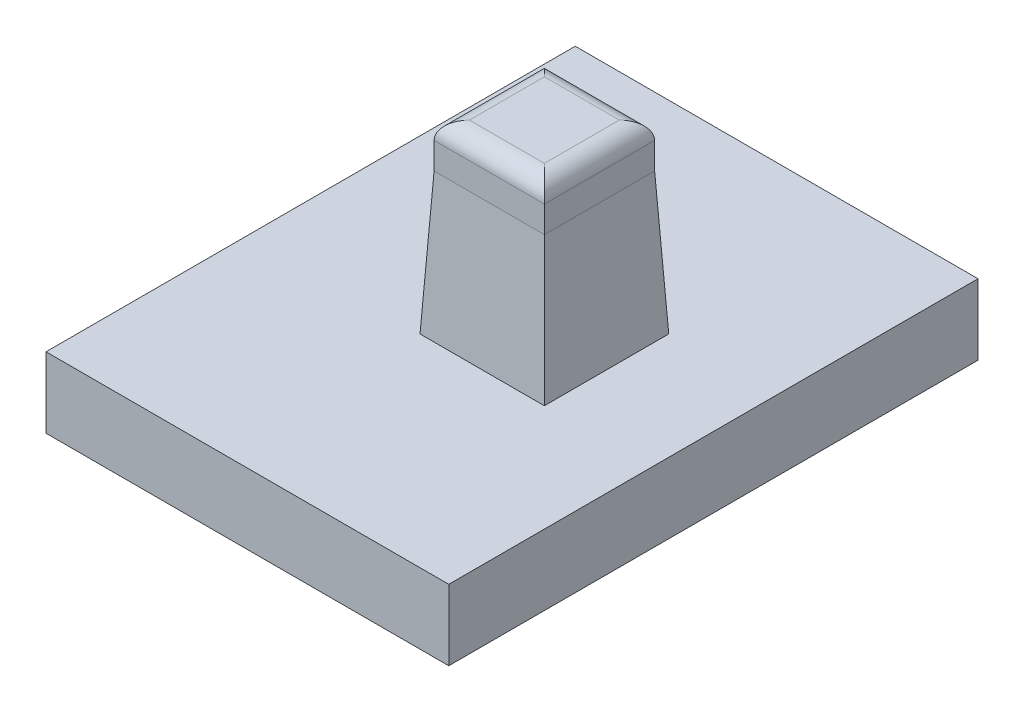
SolidWorks part; units mm, degrees
ref_plane "Front Plane" through (0, 0, 0) normal (0, 0, 1) x (1, 0, 0)
ref_plane "Top Plane" through (0, 0, 0) normal (0, 1, 0) x (1, 0, 0)
ref_plane "Right Plane" through (0, 0, 0) normal (1, 0, 0) x (0, 0, -1)
sketch "Sketch1" plane through (0, 0, 0) normal (0, 1, 0) x (1, 0, 0)
  line L0 (0, 15) -> (13.25, 15) construction
  line L1 (0, 0) -> (240, 0)
  line L2 (0, 0) -> (0, 30)
  line L3 (0, 30) -> (240, 30)
  line L4 (240, 0) -> (240, 30)
  line L5 (0, 0) -> (240, 30) construction
  line L6 (0, 30) -> (240, 0) construction
  line L7 (13.25, 15) -> (43.75, 15) construction
  line L8 (43.75, 15) -> (74.25, 15) construction
  line L9 (74.25, 15) -> (104.75, 15) construction
  line L10 (104.75, 15) -> (135.25, 15) construction
  line L11 (135.25, 15) -> (165.75, 15) construction
  line L12 (165.75, 15) -> (196.25, 15) construction
  line L14 (10.125, 18.125) -> (16.375, 18.125)
  line L15 (10.125, 18.125) -> (10.125, 11.875)
  line L16 (10.125, 11.875) -> (16.375, 11.875)
  line L17 (16.375, 18.125) -> (16.375, 11.875)
  line L18 (10.125, 18.125) -> (16.375, 11.875) construction
  line L19 (10.125, 11.875) -> (16.375, 18.125) construction
  line L23 (196.25, 15) -> (226.75, 15) construction
  line L24 (40.625, 18.125) -> (46.875, 18.125)
  line L25 (40.625, 18.125) -> (40.625, 11.875)
  line L26 (40.625, 11.875) -> (46.875, 11.875)
  line L27 (46.875, 18.125) -> (46.875, 11.875)
  line L28 (40.625, 18.125) -> (46.875, 11.875) construction
  line L29 (40.625, 11.875) -> (46.875, 18.125) construction
  line L30 (71.125, 18.125) -> (77.375, 18.125)
  line L31 (71.125, 18.125) -> (71.125, 11.875)
  line L32 (71.125, 11.875) -> (77.375, 11.875)
  line L33 (77.375, 18.125) -> (77.375, 11.875)
  line L34 (71.125, 18.125) -> (77.375, 11.875) construction
  line L35 (71.125, 11.875) -> (77.375, 18.125) construction
  line L36 (101.625, 18.125) -> (107.875, 18.125)
  line L37 (101.625, 18.125) -> (101.625, 11.875)
  line L38 (101.625, 11.875) -> (107.875, 11.875)
  line L39 (107.875, 18.125) -> (107.875, 11.875)
  line L40 (101.625, 18.125) -> (107.875, 11.875) construction
  line L41 (101.625, 11.875) -> (107.875, 18.125) construction
  line L42 (132.125, 18.125) -> (138.375, 18.125)
  line L43 (132.125, 18.125) -> (132.125, 11.875)
  line L44 (132.125, 11.875) -> (138.375, 11.875)
  line L45 (138.375, 18.125) -> (138.375, 11.875)
  line L46 (132.125, 18.125) -> (138.375, 11.875) construction
  line L47 (132.125, 11.875) -> (138.375, 18.125) construction
  line L48 (162.625, 18.125) -> (168.875, 18.125)
  line L49 (162.625, 18.125) -> (162.625, 11.875)
  line L50 (162.625, 11.875) -> (168.875, 11.875)
  line L51 (168.875, 18.125) -> (168.875, 11.875)
  line L52 (162.625, 18.125) -> (168.875, 11.875) construction
  line L53 (162.625, 11.875) -> (168.875, 18.125) construction
  line L54 (226.75, 15) -> (240, 15) construction
  line L56 (193.125, 18.125) -> (199.375, 18.125)
  line L57 (193.125, 18.125) -> (193.125, 11.875)
  line L58 (193.125, 11.875) -> (199.375, 11.875)
  line L59 (199.375, 18.125) -> (199.375, 11.875)
  line L60 (193.125, 18.125) -> (199.375, 11.875) construction
  line L61 (193.125, 11.875) -> (199.375, 18.125) construction
  line L62 (223.625, 18.125) -> (229.875, 18.125)
  line L63 (223.625, 18.125) -> (223.625, 11.875)
  line L64 (223.625, 11.875) -> (229.875, 11.875)
  line L65 (229.875, 18.125) -> (229.875, 11.875)
  line L66 (223.625, 18.125) -> (229.875, 11.875) construction
  line L67 (223.625, 11.875) -> (229.875, 18.125) construction
  point P4 (120, 15)
  point P14 (0, 15)
  point P18 (13.25, 15)
  point P24 (43.75, 15)
  point P28 (74.25, 15)
  point P33 (104.75, 15)
  point P38 (135.25, 15)
  point P43 (165.75, 15)
  point P55 (196.25, 15)
  point P56 (226.75, 15)
  dimension "D1" = 6.25
  dimension "D2" = 30.5
  dimension "D3" = 240
  dimension "D4" = 30
extrude "Boss-Extrude1" add sketch "Sketch1" along normal blind 4
sketch "Sketch2" plane through (0, 4, 0) normal (0, 1, 0) x (1, 0, 0)
  line L0 (193.125, 11.875) -> (199.375, 11.875) construction
  line L1 (10.125, 18.125) -> (16.375, 18.125)
  line L2 (10.125, 18.125) -> (10.125, 11.875)
  line L3 (10.125, 11.875) -> (16.375, 11.875)
  line L4 (16.375, 18.125) -> (16.375, 11.875)
  line L5 (10.125, 18.125) -> (16.375, 11.875) construction
  line L6 (10.125, 11.875) -> (16.375, 18.125) construction
  line L7 (40.625, 18.125) -> (46.875, 18.125)
  line L8 (40.625, 18.125) -> (40.625, 11.875)
  line L9 (40.625, 11.875) -> (46.875, 11.875)
  line L10 (46.875, 18.125) -> (46.875, 11.875)
  line L11 (40.625, 18.125) -> (46.875, 11.875) construction
  line L12 (40.625, 11.875) -> (46.875, 18.125) construction
  line L13 (71.125, 18.125) -> (77.375, 18.125)
  line L14 (71.125, 18.125) -> (71.125, 11.875)
  line L15 (71.125, 11.875) -> (77.375, 11.875)
  line L16 (77.375, 18.125) -> (77.375, 11.875)
  line L17 (71.125, 18.125) -> (77.375, 11.875) construction
  line L18 (71.125, 11.875) -> (77.375, 18.125) construction
  line L19 (101.625, 18.125) -> (107.875, 18.125)
  line L20 (101.625, 18.125) -> (101.625, 11.875)
  line L21 (101.625, 11.875) -> (107.875, 11.875)
  line L22 (107.875, 18.125) -> (107.875, 11.875)
  line L23 (101.625, 18.125) -> (107.875, 11.875) construction
  line L24 (101.625, 11.875) -> (107.875, 18.125) construction
  line L25 (132.125, 18.125) -> (138.375, 18.125)
  line L26 (132.125, 18.125) -> (132.125, 11.875)
  line L27 (132.125, 11.875) -> (138.375, 11.875)
  line L28 (138.375, 18.125) -> (138.375, 11.875)
  line L29 (132.125, 18.125) -> (138.375, 11.875) construction
  line L30 (132.125, 11.875) -> (138.375, 18.125) construction
  line L31 (162.625, 18.125) -> (168.875, 18.125)
  line L32 (162.625, 18.125) -> (162.625, 11.875)
  line L33 (162.625, 11.875) -> (168.875, 11.875)
  line L34 (168.875, 18.125) -> (168.875, 11.875)
  line L35 (162.625, 18.125) -> (168.875, 11.875) construction
  line L36 (162.625, 11.875) -> (168.875, 18.125) construction
  line L37 (193.125, 18.125) -> (199.375, 18.125)
  line L38 (193.125, 18.125) -> (193.125, 11.875)
  line L39 (193.125, 11.875) -> (199.375, 11.875)
  line L40 (199.375, 18.125) -> (199.375, 11.875)
  line L41 (193.125, 18.125) -> (199.375, 11.875) construction
  line L42 (193.125, 11.875) -> (199.375, 18.125) construction
  line L43 (223.625, 18.125) -> (229.875, 18.125)
  line L44 (223.625, 18.125) -> (223.625, 11.875)
  line L45 (223.625, 11.875) -> (229.875, 11.875)
  line L46 (229.875, 18.125) -> (229.875, 11.875)
  line L47 (223.625, 18.125) -> (229.875, 11.875) construction
  line L48 (223.625, 11.875) -> (229.875, 18.125) construction
  line L49 (199.375, 11.875) -> (199.375, 18.125) construction
  line L50 (16.375, 11.875) -> (16.375, 18.125) construction
  line L51 (10.125, 11.875) -> (16.375, 11.875) construction
  point P4 (13.25, 15)
  point P9 (43.75, 15)
  point P14 (74.25, 15)
  point P19 (104.75, 15)
  point P24 (135.25, 15)
  point P29 (165.75, 15)
  point P34 (196.25, 15)
  point P39 (226.75, 15)
extrude "Boss-Extrude2" add sketch "Sketch2" along normal blind 10.5 and the other way up to surface (4 mm away) other way up to face at (120, 0, -15)
sketch "Sketch3" plane through (0, 4, 0) normal (0, 1, 0) x (1, 0, 0)
  line L1 (22.8295, 58.4021) -> (245.0726, 58.4021)
  line L2 (22.8295, 58.4021) -> (22.8295, -37.0358)
  line L3 (22.8295, -37.0358) -> (245.0726, -37.0358)
  line L4 (245.0726, 58.4021) -> (245.0726, -37.0358)
  line L5 (22.8295, 58.4021) -> (245.0726, -37.0358) construction
  line L6 (22.8295, -37.0358) -> (245.0726, 58.4021) construction
  point P4 (133.951, 10.6831)
extrude "Cut-Extrude1" cut sketch "Sketch3" against normal through all both and the other way through all
fillet "Fillet1" radius 1 4 edges at (13.25, 14.5, -18.125) (16.375, 14.5, -15) (13.25, 14.5, -11.875) (10.125, 14.5, -15)
chamfer "Chamfer1" distance 0.4 distance2 8 4 edges at (16.375, 4, -15) (13.25, 4, -18.125) (10.125, 4, -15) (13.25, 4, -11.875)
